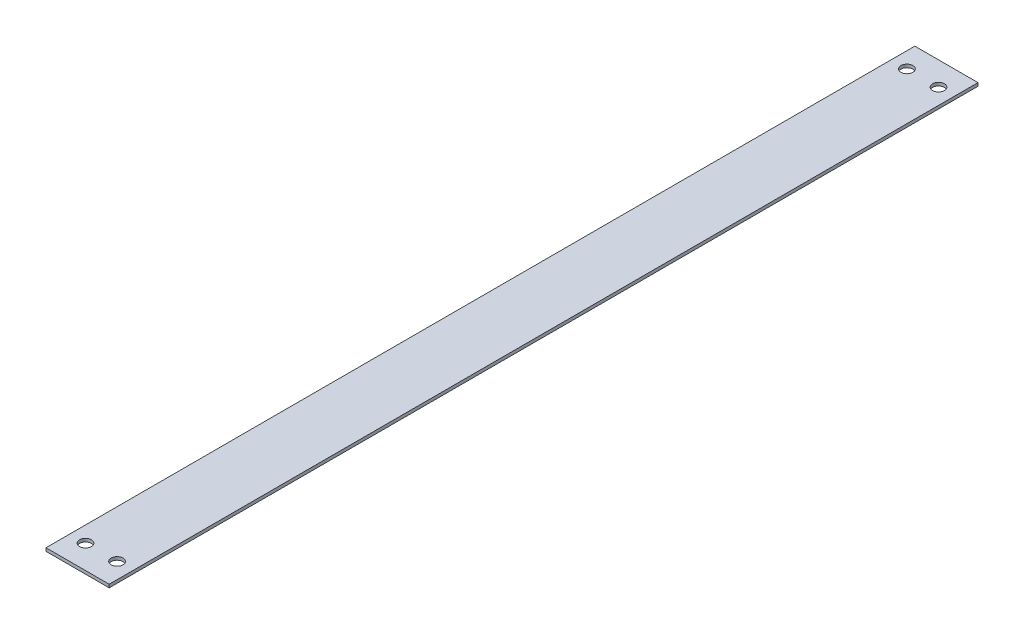
SolidWorks part; units mm, degrees
ref_plane "Front Plane" through (0, 0, 0) normal (0, 0, 1) x (1, 0, 0)
ref_plane "Top Plane" through (0, 0, 0) normal (0, 1, 0) x (1, 0, 0)
ref_plane "Right Plane" through (0, 0, 0) normal (1, 0, 0) x (0, 0, -1)
sketch "Sketch1" plane through (0, 0, 0) normal (0, 1, 0) x (1, 0, 0)
  line L1 (-25.4, -349.25) -> (25.4, -349.25)
  line L2 (-25.4, -349.25) -> (-25.4, 349.25)
  line L3 (-25.4, 349.25) -> (25.4, 349.25)
  line L4 (25.4, -349.25) -> (25.4, 349.25)
  line L5 (-25.4, -349.25) -> (25.4, 349.25) construction
  line L6 (-25.4, 349.25) -> (25.4, -349.25) construction
  point P0 (0, 0)
  dimension "D1" = 698.5
  dimension "D2" = 50.8
extrude "Boss-Extrude1" add sketch "Sketch1" along normal blind 2.54
sketch "Sketch2" plane through (0, 2.54, 0) normal (0, 1, 0) x (1, 0, 0)
  line L0 (0, 0) -> (0, 330.2) construction
  line L1 (-12.7, 330.2) -> (12.7, 330.2) construction
  line L2 (0, 0) -> (-101.3265, 0) construction
  line L3 (-12.7, -330.2) -> (12.7, -330.2) construction
  circle A0 centre (-12.7, 330.2) radius 4.7625
  circle A1 centre (12.7, 330.2) radius 4.7625
  circle A2 centre (12.7, -330.2) radius 4.7625
  circle A3 centre (-12.7, -330.2) radius 4.7625
  point P6 (0, 330.2)
  point P13 (0, -330.2)
  dimension "D2" = 9.525
  dimension "D1" = 25.4
  dimension "D3" = 330.2
extrude "Cut-Extrude1" cut sketch "Sketch2" against normal through all both and the other way through all
